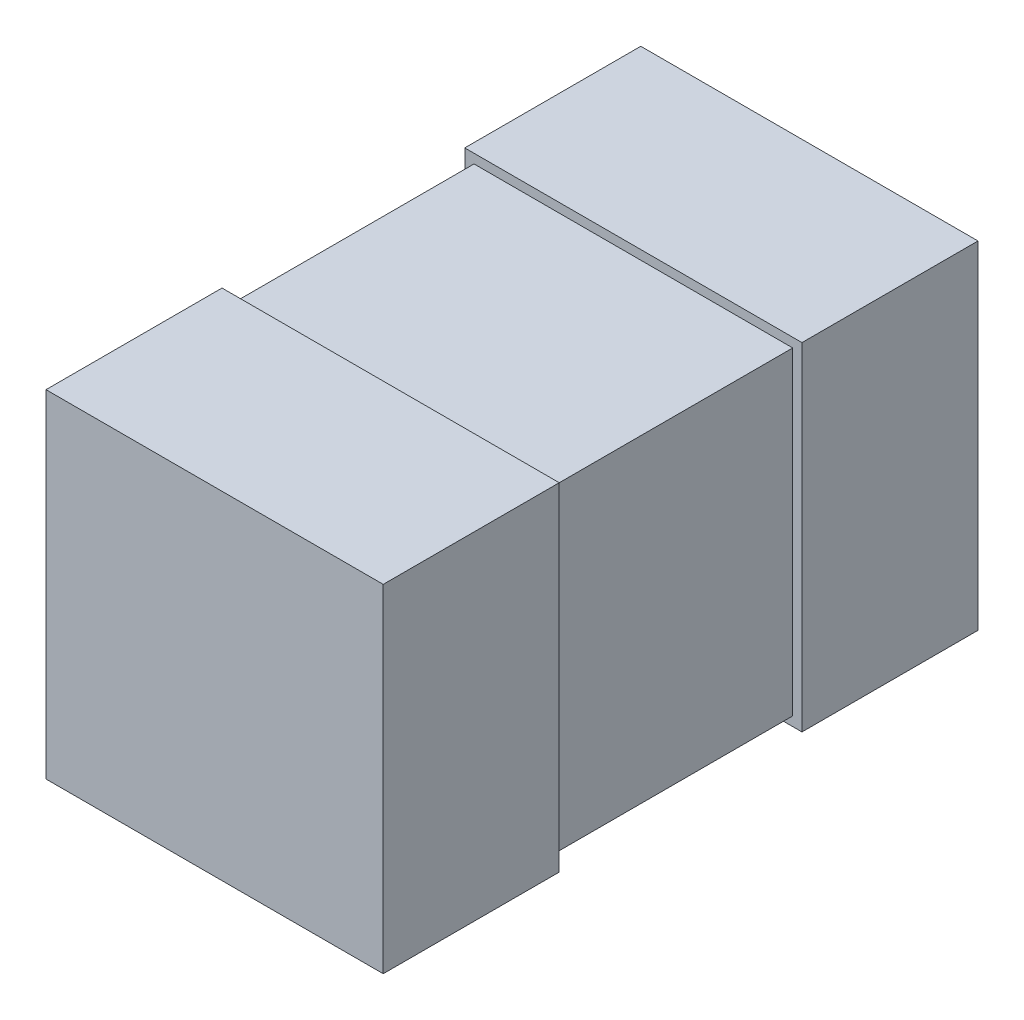
SolidWorks part; units mm, degrees
ref_plane "Front Plane" through (0, 0, 0) normal (0, 0, 1) x (1, 0, 0)
ref_plane "Top Plane" through (0, 0, 0) normal (0, 1, 0) x (1, 0, 0)
ref_plane "Right Plane" through (0, 0, 0) normal (1, 0, 0) x (0, 0, -1)
sketch "Sketch2" plane through (0, 0, 0) normal (0, 1, 0) x (1, 0, 0)
  line L1 (-0.91, -1.605) -> (0.91, -1.605)
  line L2 (-0.91, -1.605) -> (-0.91, -0.655)
  line L3 (-0.91, -0.655) -> (0.91, -0.655)
  line L4 (0.91, -1.605) -> (0.91, -0.655)
extrude "Boss-Extrude1" add sketch "Sketch2" along normal blind 1.82
sketch "Sketch4" plane through (0, 0, 0.655) normal (0, 0, -1) x (-1, 0, 0)
  line L1 (0.86, 0.05) -> (-0.86, 0.05)
  line L2 (0.86, 0.05) -> (0.86, 1.77)
  line L3 (0.86, 1.77) -> (-0.86, 1.77)
  line L4 (-0.86, 0.05) -> (-0.86, 1.77)
extrude "Boss-Extrude2" add sketch "Sketch4" along normal blind 1.31 separate body
sketch "Sketch5" plane through (0, 0, -0.655) normal (0, 0, -1) x (-1, 0, 0)
  line L0 (-0.91, 1.82) -> (-0.91, 0) construction
  line L1 (0.91, 1.82) -> (-0.91, 1.82)
  line L2 (0.91, 1.82) -> (0.91, 0)
  line L3 (0.91, 0) -> (-0.91, 0)
  line L4 (-0.91, 1.82) -> (-0.91, 0)
extrude "Boss-Extrude3" add sketch "Sketch5" along normal blind 0.95 separate body
ref_plane "Plane1" through (0, 0, 0) normal (0, 1, 0) x (-1, 0, 0)
ref_plane "Plane2" through (0.91, 0, 0) normal (1, 0, 0) x (0, 0, -1)
ref_plane "Plane3" through (0, 0, -1.605) normal (0, 0, 1) x (1, 0, 0)
